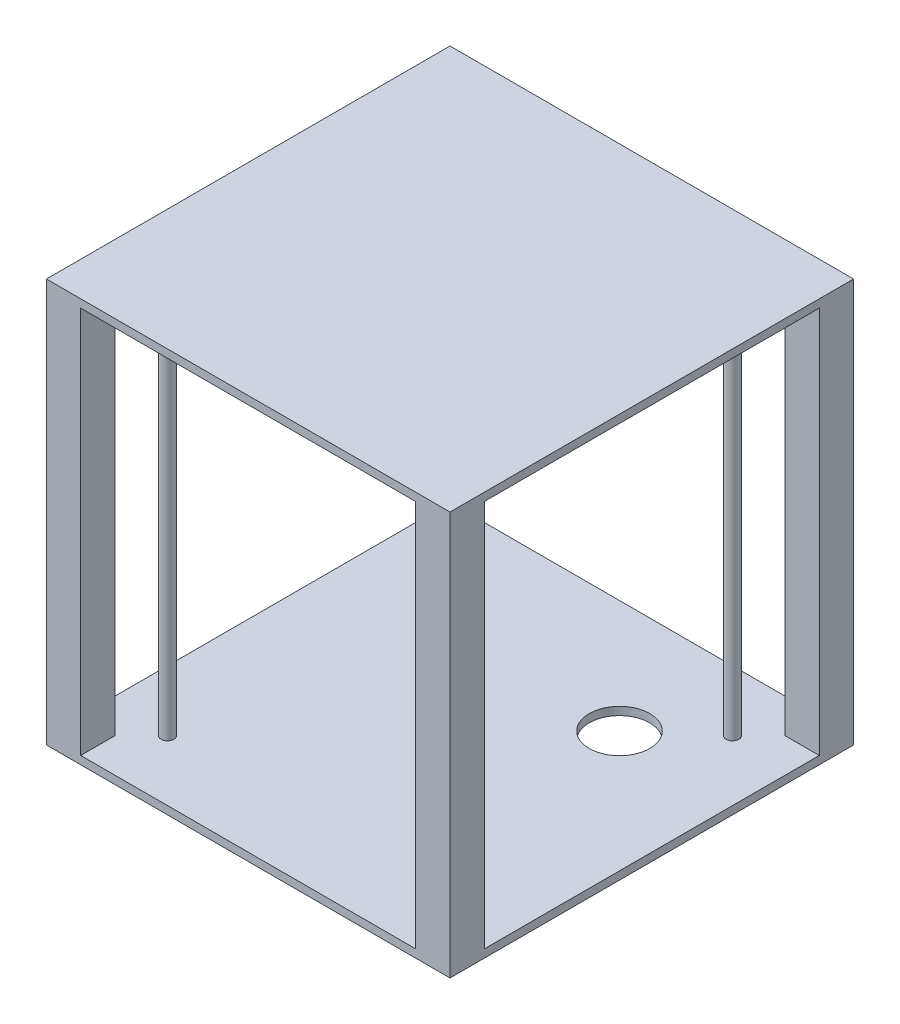
SolidWorks part; units mm, degrees
ref_plane "Front Plane" through (0, 0, 0) normal (0, 0, 1) x (1, 0, 0)
ref_plane "Top Plane" through (0, 0, 0) normal (0, 1, 0) x (1, 0, 0)
ref_plane "Right Plane" through (0, 0, 0) normal (1, 0, 0) x (0, 0, -1)
sketch "Sketch1" plane through (0, 0, 0) normal (0, 1, 0) x (1, 0, 0)
  line L1 (0, 0) -> (100, 0)
  line L2 (0, 0) -> (0, 100)
  line L3 (0, 100) -> (100, 100)
  line L4 (100, 0) -> (100, 100)
  dimension "D1" = 100
  dimension "D2" = 100
extrude "Base" add sketch "Sketch1" along normal blind 2
sketch "Sketch2" plane through (0, 2, 0) normal (0, 1, 0) x (1, 0, 0)
  line L1 (0, 0) -> (8.5, 0)
  line L2 (0, 0) -> (0, 8.5)
  line L3 (0, 8.5) -> (8.5, 8.5)
  line L4 (8.5, 0) -> (8.5, 8.5)
  dimension "D1" = 8.5
  dimension "D2" = 8.5
extrude "Boss-Extrude2" add sketch "Sketch2" along normal blind 96
pattern_linear "LPattern1" count 2 spacing 91.5 along (0, 0, -1) count 2 spacing 91.5 along (1, 0, 0) of "Boss-Extrude2"
pattern_linear "LPattern2" count 2 spacing 98 along (0, 1, 0) of "Base"
sketch "Sketch3" plane through (0, 2, 0) normal (0, 1, 0) x (1, 0, 0)
  line L0 (0, 91.5) -> (0, 8.5) construction
  line L1 (91.5, 100) -> (8.5, 100) construction
  circle A0 centre (15, 85) radius 1.575
  dimension "D3" = 3.15
  dimension "D1" = 15
  dimension "D2" = 15
extrude "Rods" add sketch "Sketch3" along normal blind 96
pattern_linear "LPattern3" count 2 spacing 70 along (1, 0, 0) count 2 spacing 70 along (0, 0, 1) of "Rods"
sketch "Sketch5" plane through (0, 2, 0) normal (0, 1, 0) x (1, 0, 0)
  circle A0 centre (70, 72) radius 7.5
  dimension "D1" = 15
extrude "Cut-Extrude1" cut sketch "Sketch5" against normal blind 10
